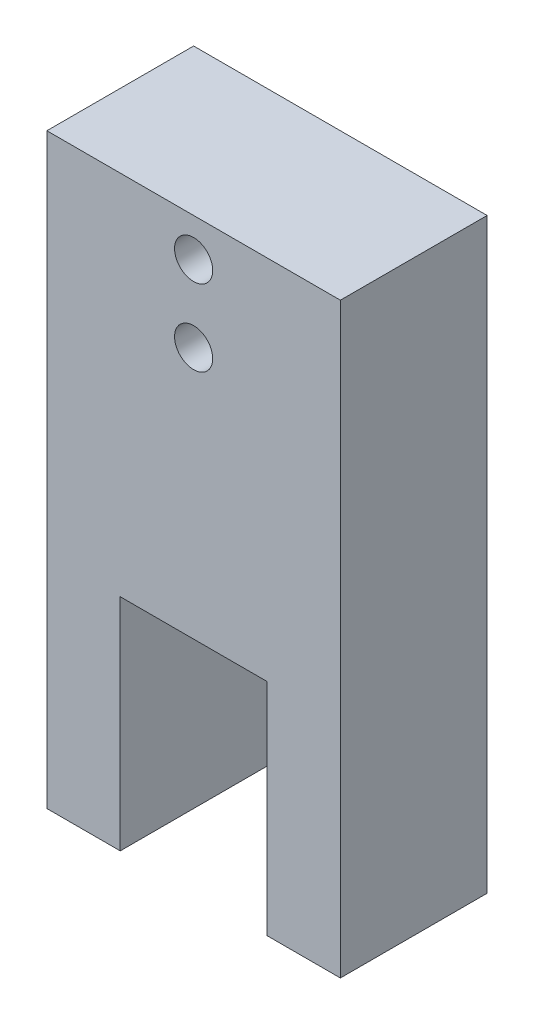
SolidWorks part; units mm, degrees
ref_plane "Front Plane" through (0, 0, 0) normal (0, 0, 1) x (1, 0, 0)
ref_plane "Top Plane" through (0, 0, 0) normal (0, 1, 0) x (1, 0, 0)
ref_plane "Right Plane" through (0, 0, 0) normal (1, 0, 0) x (0, 0, -1)
sketch "Sketch2" plane through (0, 0, 0) normal (0, 0, 1) x (1, 0, 0)
  line L1 (0, 0) -> (50.8, 0)
  line L2 (0, 0) -> (0, 101.6)
  line L3 (0, 101.6) -> (50.8, 101.6)
  line L4 (50.8, 0) -> (50.8, 101.6)
  line L5 (12.7, 0) -> (38.1, 0)
  line L6 (12.7, 0) -> (12.7, 38.1)
  line L7 (12.7, 38.1) -> (38.1, 38.1)
  line L8 (38.1, 0) -> (38.1, 38.1)
  circle A0 centre (25.4, 94.996) radius 3.302
  circle A1 centre (25.4, 81.788) radius 3.302
  dimension "D4" = 6.604
  dimension "D8" = 6.604
  dimension "D1" = 101.6
  dimension "D2" = 50.8
  dimension "D3" = 6.604
  dimension "D5" = 25.4
  dimension "D6" = 13.208
  dimension "D7" = 25.4
  dimension "D9" = 25.4
  dimension "D10" = 38.1
  dimension "D11" = 12.7
extrude "Boss-Extrude1" add sketch "Sketch2" along normal blind 25.4 contours L8 L1 L4 L3 L2 L6 L7 A1 A0
